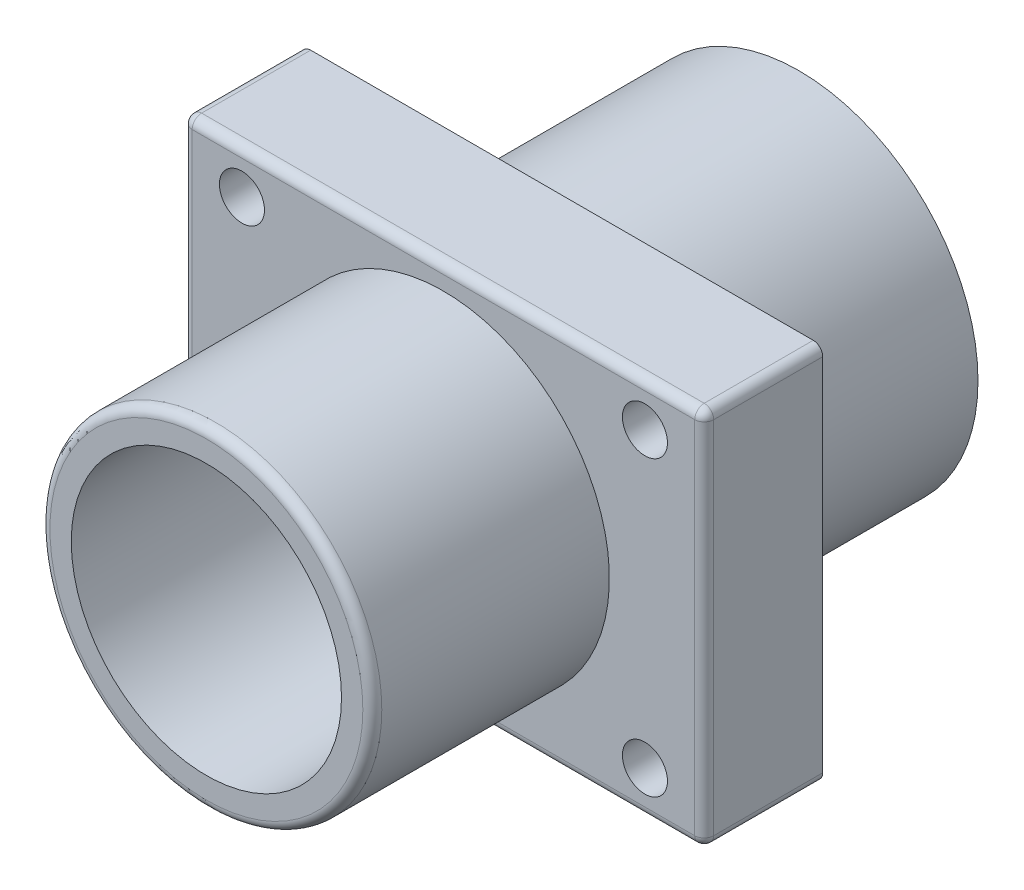
SolidWorks part; units mm, degrees
ref_plane "Front Plane" through (0, 0, 0) normal (0, 0, 1) x (1, 0, 0)
ref_plane "Top Plane" through (0, 0, 0) normal (0, 1, 0) x (1, 0, 0)
ref_plane "Right Plane" through (0, 0, 0) normal (1, 0, 0) x (0, 0, -1)
sketch "Sketch1" plane through (0, 0, 0) normal (0, 0, 1) x (1, 0, 0)
  line L1 (-55, -40) -> (55, -40)
  line L2 (-55, -40) -> (-55, 40)
  line L3 (-55, 40) -> (55, 40)
  line L4 (55, -40) -> (55, 40)
  line L5 (-55, -40) -> (55, 40) construction
  line L6 (-55, 40) -> (55, -40) construction
  point P0 (0, 0)
  dimension "D1" = 110
  dimension "D2" = 80
extrude "Boss-Extrude1" add sketch "Sketch1" along normal blind 25
sketch "Sketch2" plane through (0, 0, 25) normal (0, 0, 1) x (1, 0, 0)
  line L0 (-55, 40) -> (-55, -40) construction
  line L1 (-55, -40) -> (55, -40) construction
  circle A0 centre (-42.5, -30.9) radius 4.75
  point P4 (0, 0)
  dimension "D1" = 9.5
  dimension "D2" = 12.5
  dimension "D3" = 9.1
extrude "Cut-Extrude1" cut sketch "Sketch2" against normal blind 25
pattern_linear "LPattern1" count 2 spacing 85 along (1, 0, 0) count 2 spacing 61.8 along (0, 1, 0) of "Cut-Extrude1"
sketch "Sketch3" plane through (0, 0, 25) normal (0, 0, 1) x (1, 0, 0)
  circle A0 centre (0, 0) radius 35
  dimension "D1" = 70
extrude "Boss-Extrude2" add sketch "Sketch3" along normal blind 50
sketch "Sketch4" plane through (0, 0, 0) normal (0, 0, -1) x (-1, 0, 0)
  circle A0 centre (0, 0) radius 37.75
  dimension "D1" = 75.5
extrude "Boss-Extrude3" add sketch "Sketch4" along normal blind 50
sketch "Sketch5" plane through (0, 0, 75) normal (0, 0, 1) x (1, 0, 0)
  circle A0 centre (0, 0) radius 28.5
  dimension "D1" = 57
extrude "Cut-Extrude2" cut sketch "Sketch5" against normal blind 75
sketch "Sketch6" plane through (0, 0, 0) normal (0, 0, 1) x (1, 0, 0)
  circle A0 centre (0, 0) radius 23
  dimension "D1" = 46
extrude "Cut-Extrude3" cut sketch "Sketch6" against normal blind 50
fillet "Fillet1" radius 2 9 edges at (35, 0, 75) (-55, 40, 12.5) (-55, -40, 12.5) (55, 40, 12.5) (55, -40, 12.5) (0, -40, 25) (-55, 0, 25) (0, 40, 25) (55, 0, 25)
